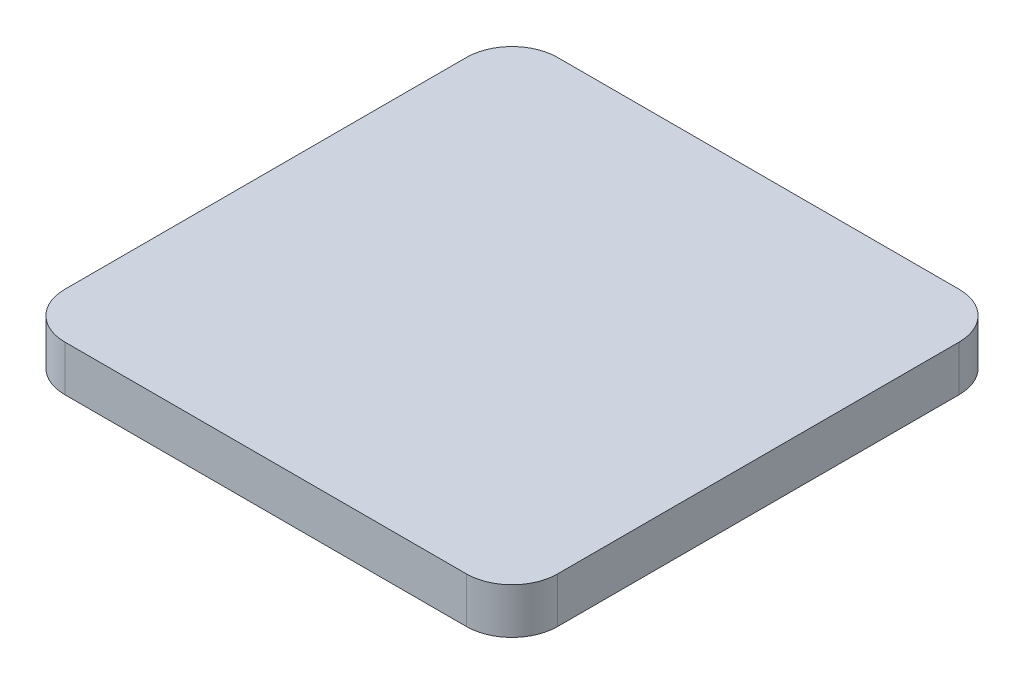
SolidWorks part; units mm, degrees
ref_plane "前视基准面" through (0, 0, 0) normal (0, 0, 1) x (1, 0, 0)
ref_plane "上视基准面" through (0, 0, 0) normal (0, 1, 0) x (1, 0, 0)
ref_plane "右视基准面" through (0, 0, 0) normal (1, 0, 0) x (0, 0, -1)
sketch "草图1" plane through (0, 0, 0) normal (0, 1, 0) x (1, 0, 0)
  line L1 (-27, 27) -> (27, 27)
  line L2 (-27, 27) -> (-27, -27)
  line L3 (-27, -27) -> (27, -27)
  line L4 (27, 27) -> (27, -27)
  line L5 (-27, 27) -> (27, -27) construction
  line L6 (-27, -27) -> (27, 27) construction
  point P0 (0, 0)
extrude "凸台-拉伸2" add sketch "草图1" along normal blind 5
fillet "圆角1" radius 5 4 edges at (-27, 2.5, 27) (-27, 2.5, -27) (27, 2.5, -27) (27, 2.5, 27)
